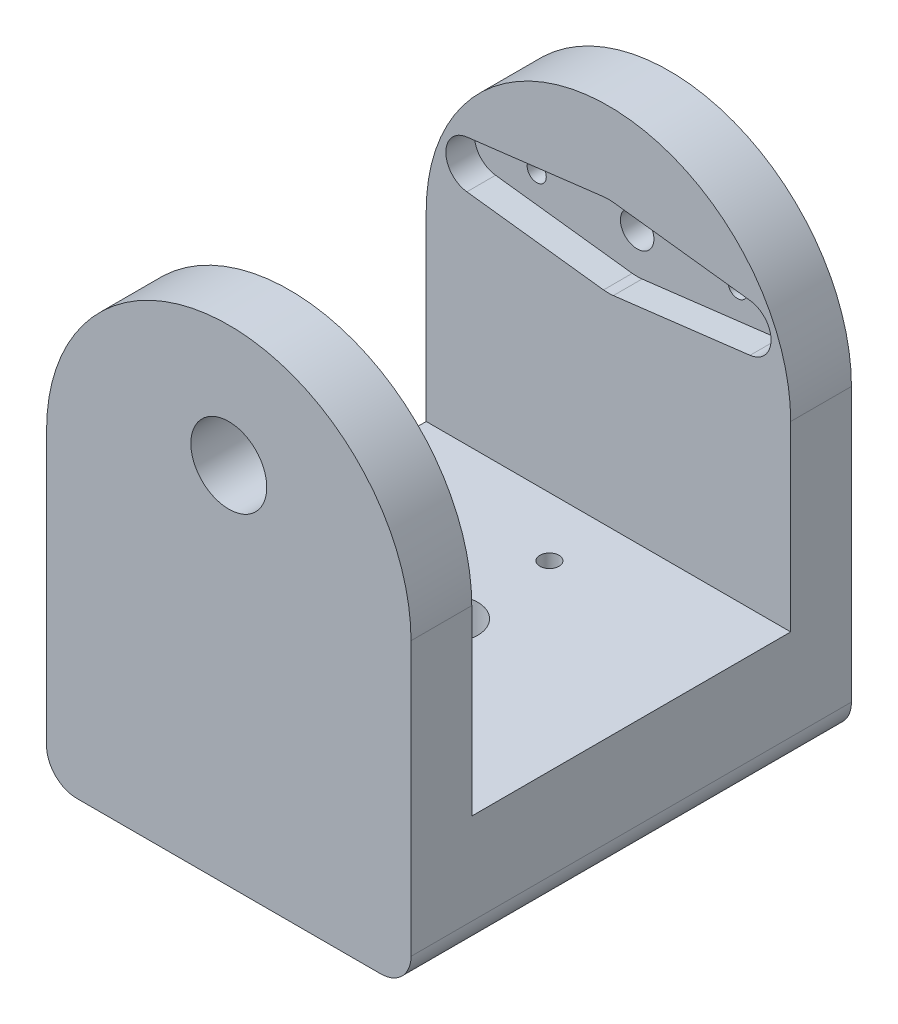
SolidWorks part; units mm, degrees
ref_plane "Front Plane" through (0, 0, 0) normal (0, 0, 1) x (1, 0, 0)
ref_plane "Top Plane" through (0, 0, 0) normal (0, 1, 0) x (1, 0, 0)
ref_plane "Right Plane" through (0, 0, 0) normal (1, 0, 0) x (0, 0, -1)
sketch "Sketch1" plane through (0, 0, 0) normal (0, 0, 1) x (1, 0, 0)
  line L1 (0, 0) -> (38.1, 0)
  line L2 (0, 0) -> (0, 31.75)
  line L4 (38.1, 0) -> (38.1, 31.75)
  arc A0 (0, 31.75) -> (38.1, 31.75) centre (19.05, 31.75) cw
  dimension "D1" = 38.1
  dimension "D2" = 31.75
extrude "Boss-Extrude1" add sketch "Sketch1" along normal blind 46.0375
fillet "Fillet1" radius 3.175 2 edges at (0, 0, 23.0188) (38.1, 0, 23.0188)
ref_plane "Plane1" through (0, 0, 23.0188) normal (0, 0, -1) x (-1, 0, 0)
sketch "Sketch2" plane through (0, 0, 23.0188) normal (0, 0, -1) x (-1, 0, 0)
  line L0 (-38.1, 31.75) -> (-38.1, 12.7)
  line L1 (-38.1, 12.7) -> (0, 12.7)
  line L2 (0, 12.7) -> (0, 31.75)
  arc A0 (0, 31.75) -> (-38.1, 31.75) centre (-19.05, 31.75) ccw construction
  arc A1 (0, 31.75) -> (-38.1, 31.75) centre (-19.05, 31.75) ccw
  dimension "D1" = 19.05
extrude "Cut-Extrude1" cut sketch "Sketch2" against normal mid plane 33.3375
sketch "Sketch3" plane through (0, 0, 6.35) normal (0, 0, 1) x (1, 0, 0)
  circle A0 centre (19.05, 38.1) radius 10.5 construction
  arc A1 (38.1, 31.75) -> (0, 31.75) centre (19.05, 31.75) ccw construction
  arc A2 (38.1, 31.75) -> (0, 31.75) centre (19.05, 31.75) ccw construction
  circle A3 centre (8.55, 38.1) radius 1
  circle A4 centre (29.55, 38.1) radius 1
  circle A5 centre (19.05, 38.1) radius 1.75
  dimension "D2" = 21
  dimension "D3" = 2
  dimension "D4" = 3.5
  dimension "D1" = 6.35
extrude "Cut-Extrude2" cut sketch "Sketch3" against normal up to surface (6.35 mm away) up to face at (19.05, 14.5975, 0)
sketch "Sketch4" plane through (0, 0, 39.6875) normal (0, 0, -1) x (-1, 0, 0)
  arc A0 (0, 31.75) -> (-38.1, 31.75) centre (-19.05, 31.75) ccw construction
  arc A1 (0, 31.75) -> (-38.1, 31.75) centre (-19.05, 31.75) ccw construction
  circle A2 centre (-19.05, 38.1) radius 3.9688
  dimension "D2" = 7.9375
  dimension "D1" = 6.35
extrude "Cut-Extrude3" cut sketch "Sketch4" against normal up to surface (6.35 mm away) up to face at (19.05, 14.5975, 46.0375)
sketch "Sketch5" plane through (0, 0, 0) normal (0, -1, 0) x (1, 0, 0)
  line L0 (3.175, 0) -> (34.925, 0) construction
  line L1 (3.175, 46.0375) -> (34.925, 46.0375) construction
  line L2 (3.175, 0) -> (34.925, 0) construction
  line L3 (3.175, 46.0375) -> (34.925, 46.0375) construction
  line L4 (19.05, 46.0375) -> (19.05, 0) construction
  line L5 (23.2667, 22.4875) -> (21.5304, 8.7063)
  line L6 (16.5696, 8.7063) -> (14.8333, 22.4875)
  line L7 (21.5304, 37.3313) -> (23.2667, 23.55)
  line L8 (14.8333, 23.55) -> (16.5696, 37.3313)
  arc A1 (14.8333, 23.55) -> (14.8333, 22.4875) centre (19.05, 23.0188) ccw
  circle A2 centre (19.05, 23.0188) radius 14 construction
  arc A3 (16.5696, 8.7063) -> (21.5304, 8.7063) centre (19.05, 9.0188) ccw
  arc A4 (21.5304, 37.3313) -> (16.5696, 37.3313) centre (19.05, 37.0188) ccw
  arc A5 (23.2667, 22.4875) -> (23.2667, 23.55) centre (19.05, 23.0188) ccw
  dimension "D1" = 8.5
  dimension "D2" = 28
  dimension "D3" = 5
extrude "Cut-Extrude4" cut sketch "Sketch5" against normal blind 3
sketch "Sketch6" plane through (0, 3, 0) normal (0, -1, 0) x (1, 0, 0)
  arc A0 (23.2667, 22.4875) -> (23.2667, 23.55) centre (19.05, 23.0188) ccw construction
  arc A1 (23.2667, 22.4875) -> (23.2667, 23.55) centre (19.05, 23.0188) ccw construction
  circle A2 centre (19.05, 23.0188) radius 1.75
  circle A3 centre (19.05, 23.0188) radius 10.5 construction
  circle A4 centre (19.05, 33.5188) radius 1
  circle A5 centre (19.05, 12.5188) radius 1
  dimension "D1" = 3.5
  dimension "D2" = 21
  dimension "D3" = 2
extrude "Cut-Extrude5" cut sketch "Sketch6" against normal up to surface (9.7 mm away) up to face at (19.05, 12.7, 23.0188)
sketch "Sketch7" plane through (0, 12.7, 0) normal (0, 1, 0) x (1, 0, 0)
  circle A0 centre (19.05, -23.0188) radius 3
  dimension "D1" = 6
extrude "Cut-Extrude6" cut sketch "Sketch7" against normal blind 6.35
sketch "Sketch9" plane through (0, 0, 6.35) normal (0, 0, 1) x (1, 0, 0)
  line L0 (4.2483, 40.5817) -> (18.5371, 42.3189)
  line L1 (19.5629, 42.3189) -> (33.8517, 40.5817)
  line L2 (33.8517, 35.6183) -> (19.5629, 33.8811)
  line L3 (18.5371, 33.8811) -> (4.2483, 35.6183)
  circle A1 centre (19.05, 38.1) radius 14.5 construction
  circle A2 centre (8.55, 38.1) radius 1 construction
  circle A3 centre (29.55, 38.1) radius 1 construction
  circle A4 centre (19.05, 38.1) radius 1.75 construction
  circle A5 centre (8.55, 38.1) radius 1
  circle A6 centre (29.55, 38.1) radius 1
  circle A7 centre (19.05, 38.1) radius 1.75
  arc A8 (33.8517, 35.6183) -> (33.8517, 40.5817) centre (33.55, 38.1) ccw
  arc A9 (4.2483, 40.5817) -> (4.2483, 35.6183) centre (4.55, 38.1) ccw
  arc A10 (18.5371, 33.8811) -> (19.5629, 33.8811) centre (19.05, 38.1) ccw
  arc A11 (19.5629, 42.3189) -> (18.5371, 42.3189) centre (19.05, 38.1) ccw
  dimension "D1" = 29
  dimension "D2" = 5
  dimension "D3" = 8.5
extrude "Cut-Extrude7" cut sketch "Sketch9" against normal blind 3
